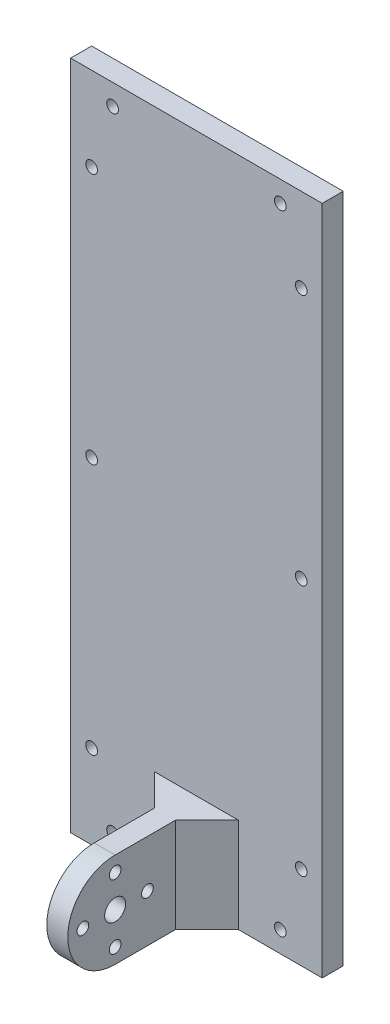
SolidWorks part; units mm, degrees
material "Copper"
ref_plane "Front Plane" through (0, 0, 0) normal (0, 0, 1) x (1, 0, 0)
ref_plane "Top Plane" through (0, 0, 0) normal (0, 1, 0) x (1, 0, 0)
ref_plane "Right Plane" through (0, 0, 0) normal (1, 0, 0) x (0, 0, -1)
sketch "Sketch1" plane through (0, 0, 0) normal (0, 0, 1) x (1, 0, 0)
  line L1 (0, 0) -> (76.2, 0)
  line L2 (0, 0) -> (0, 203.2)
  line L3 (0, 203.2) -> (76.2, 203.2)
  line L4 (76.2, 0) -> (76.2, 203.2)
  dimension "D1" = 76.2
  dimension "D2" = 203.2
extrude "Boss-Extrude1" add sketch "Sketch1" along normal blind 6.35
sketch "Sketch2" plane through (0, 0, 6.35) normal (0, 0, 1) x (1, 0, 0)
  line L0 (76.2, 0) -> (76.2, 203.2) construction
  line L1 (34.925, 28.702) -> (41.275, 28.702)
  line L2 (34.925, 28.702) -> (34.925, 0)
  line L3 (34.925, 0) -> (41.275, 0)
  line L4 (41.275, 28.702) -> (41.275, 0)
  line L5 (0, 203.2) -> (0, 0) construction
  point P6 (76.2, 101.6)
  point P7 (41.275, 14.351)
  point P8 (38.1, 0)
  dimension "D1" = 6.35
  dimension "D2" = 28.702
  dimension "D3" = 87.249
  dimension "D4" = 38.1
extrude "Boss-Extrude2" add sketch "Sketch2" along normal blind 44.45
sketch "Sketch3" plane through (41.275, 0, 0) normal (1, 0, 0) x (0, 0, -1)
  line L0 (-6.35, 0) -> (-6.35, 203.2) construction
  line L1 (-50.8, 0) -> (-6.35, 0) construction
  circle A0 centre (-34.1546, 14.351) radius 3.175
  dimension "D1" = 27.8046
  dimension "D2" = 6.35
  dimension "D3" = 14.351
extrude "Cut-Extrude1" cut sketch "Sketch3" against normal blind 6.35
sketch "Sketch4" plane through (41.275, 0, 0) normal (1, 0, 0) x (0, 0, -1)
  line L0 (-50.8, 0) -> (-6.35, 0) construction
  circle A0 centre (-43.9336, 14.351) radius 1.778
  circle A1 centre (-34.1546, 14.351) radius 3.175 construction
  dimension "D1" = 3.556
  dimension "D2" = 14.351
  dimension "D3" = 9.779
extrude "Cut-Extrude2" cut sketch "Sketch4" against normal blind 6.35
pattern_circular "CirPattern1" count 4 over 360 about axis through (0, 14.351, 34.1546) along (1, 0, 0) of "Cut-Extrude2"
sketch "Sketch5" plane through (41.275, 0, 0) normal (1, 0, 0) x (0, 0, -1)
  circle A0 centre (-34.1546, 14.351) radius 14.351
  line M8 (-6.35, 28.702) -> (-50.8, 28.702)
  line M9 (-50.8, 28.702) -> (-50.8, 0)
  line M10 (-50.8, 0) -> (-6.35, 0)
  dimension "D1" = 28.702
extrude "Cut-Extrude3" cut sketch "Sketch5" against normal blind 6.35 contours A0 M8 M9 M10
sketch "Sketch6" plane through (0, 0, 0) normal (0, 0, -1) x (-1, 0, 0)
  line L0 (0, 0) -> (-76.2, 0) construction
  line L1 (-76.2, 0) -> (-76.2, 203.2) construction
  line L2 (-76.2, 203.2) -> (0, 203.2) construction
  line L3 (0, 203.2) -> (0, 0) construction
  circle A0 centre (-63.5, 6.35) radius 1.778
  circle A1 centre (-12.7, 6.35) radius 1.778
  circle A2 centre (-6.35, 177.8) radius 1.778
  circle A3 centre (-6.35, 25.4) radius 1.778
  circle A4 centre (-69.85, 25.4) radius 1.778
  circle A5 centre (-69.85, 177.8) radius 1.778
  circle A6 centre (-63.5, 196.85) radius 1.778
  circle A7 centre (-12.7, 196.85) radius 1.778
  circle A8 centre (-6.35, 101.6) radius 1.778
  circle A9 centre (-69.85, 101.6) radius 1.778
  dimension "D1" = 3.556
  dimension "D4" = 50.8
  dimension "D5" = 12.7
  dimension "D6" = 6.35
  dimension "D8" = 50.8
  dimension "D9" = 12.7
  dimension "D11" = 6.35
  dimension "D16" = 152.4
  dimension "D17" = 25.4
  dimension "D18" = 3.556
  dimension "D19" = 3.556
  dimension "D2" = 6.35
  dimension "D3" = 6.35
  dimension "D7" = 6.35
  dimension "D10" = 6.35
  dimension "D12" = 152.4
  dimension "D13" = 25.4
  dimension "D14" = 6.35
  dimension "D15" = 6.35
  dimension "D20" = 6.35
  dimension "D21" = 6.35
  dimension "D22" = 76.2
  dimension "D23" = 76.2
extrude "Cut-Extrude4" cut sketch "Sketch6" against normal blind 6.35
sketch "Sketch8" plane through (0, 0, 0) normal (0, -1, 0) x (1, 0, 0)
  line L0 (41.275, 6.35) -> (41.275, 15.875)
  line L1 (41.275, 34.1546) -> (41.275, 6.35) construction
  line L2 (41.275, 15.875) -> (50.8, 6.35)
  line L3 (41.275, 6.35) -> (76.2, 6.35) construction
  line L4 (50.8, 6.35) -> (41.275, 6.35)
  line L5 (34.925, 6.35) -> (34.925, 15.875)
  line L6 (34.925, 34.1546) -> (34.925, 6.35) construction
  line L7 (34.925, 15.875) -> (25.4, 6.35)
  line L8 (0, 6.35) -> (34.925, 6.35) construction
  line L9 (25.4, 6.35) -> (34.925, 6.35)
  dimension "D1" = 9.525
  dimension "D2" = 9.525
  dimension "D3" = 9.525
  dimension "D4" = 9.525
extrude "Boss-Extrude3" add sketch "Sketch8" against normal up to surface (28.702 mm away) up to face at (38.1, 28.702, 20.2523)
